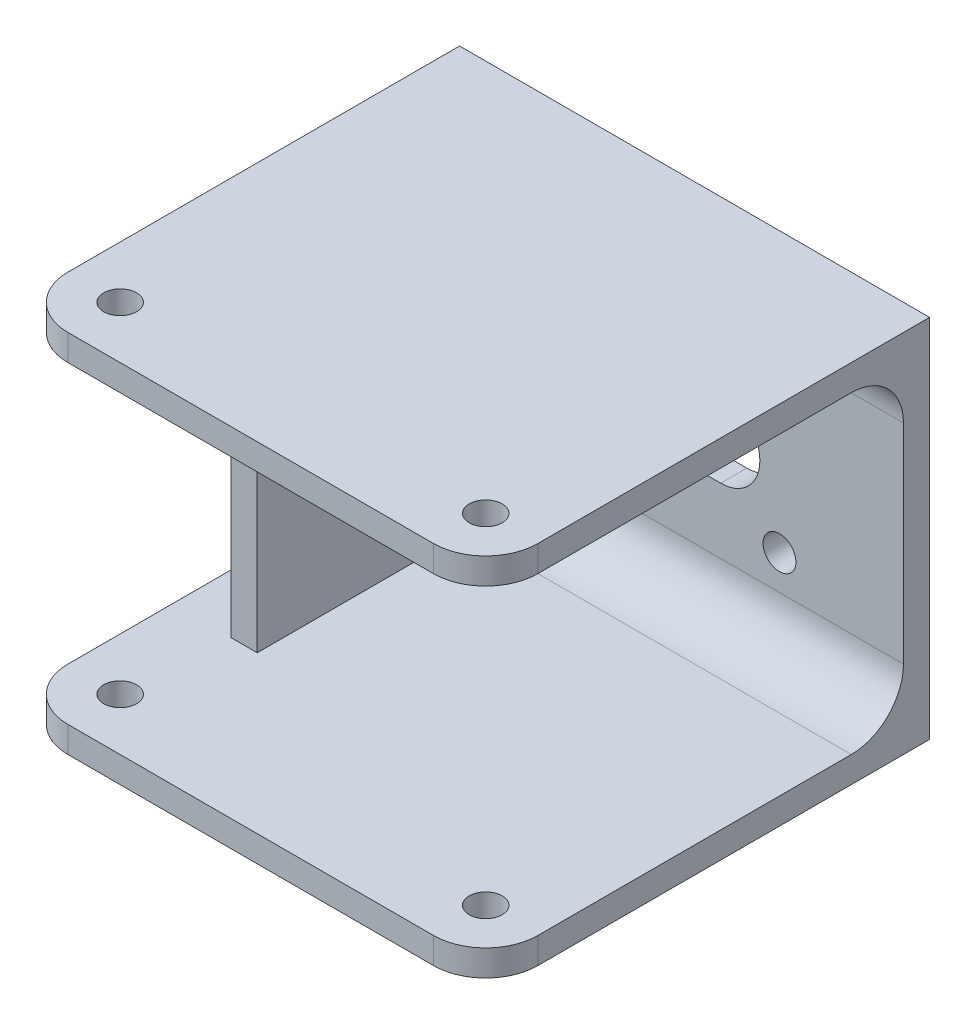
SolidWorks part; units mm, degrees
ref_plane "Front Plane" through (0, 0, 0) normal (0, 0, 1) x (1, 0, 0)
ref_plane "Top Plane" through (0, 0, 0) normal (0, 1, 0) x (1, 0, 0)
ref_plane "Right Plane" through (0, 0, 0) normal (1, 0, 0) x (0, 0, -1)
sketch "Sketch1" plane through (0, 0, 0) normal (0, 0, 1) x (1, 0, 0)
  line L1 (-28.575, -19.05) -> (28.575, -19.05)
  line L2 (-28.575, -19.05) -> (-28.575, 19.05)
  line L3 (-28.575, 19.05) -> (28.575, 19.05)
  line L4 (28.575, -19.05) -> (28.575, 19.05)
  line L5 (-28.575, -19.05) -> (28.575, 19.05) construction
  line L6 (-28.575, 19.05) -> (28.575, -19.05) construction
  point P0 (0, 0)
  dimension "D1" = 38.1
  dimension "D2" = 57.15
extrude "Boss-Extrude1" add sketch "Sketch1" along normal blind 3.175
sketch "Sketch2" plane through (0, 0, 3.175) normal (0, 0, 1) x (1, 0, 0)
  line L0 (-6.35, 0) -> (6.35, 0) construction
  line L1 (-6.35, 4.7625) -> (6.35, 4.7625)
  line L2 (-6.35, -4.7625) -> (6.35, -4.7625)
  line L4 (-13.5, -8.5) -> (13.5, -8.5) construction
  line L5 (-13.5, -8.5) -> (-13.5, 8.5) construction
  line L6 (-13.5, 8.5) -> (13.5, 8.5) construction
  line L7 (13.5, -8.5) -> (13.5, 8.5) construction
  line L8 (-13.5, -8.5) -> (13.5, 8.5) construction
  line L9 (-13.5, 8.5) -> (13.5, -8.5) construction
  arc A0 (-6.35, 4.7625) -> (-6.35, -4.7625) centre (-6.35, 0) ccw
  arc A1 (6.35, -4.7625) -> (6.35, 4.7625) centre (6.35, 0) ccw
  circle A2 centre (-13.5, 8.5) radius 2
  circle A3 centre (13.5, 8.5) radius 2
  circle A4 centre (13.5, -8.5) radius 2
  circle A5 centre (-13.5, -8.5) radius 2
  point P2 (0, 0)
  point P8 (0, 0)
  dimension "D2" = 4.7625
  dimension "D5" = 4
  dimension "D1" = 12.7
  dimension "D3" = 27
  dimension "D4" = 17
extrude "Cut-Extrude1" cut sketch "Sketch2" against normal through all
sketch "Sketch3" plane through (0, 0, 3.175) normal (0, 0, 1) x (1, 0, 0)
  line L0 (-28.575, 19.05) -> (-28.575, -19.05) construction
  line L1 (28.575, 19.05) -> (-28.575, 19.05)
  line L2 (28.575, 19.05) -> (28.575, 22.225)
  line L3 (28.575, 22.225) -> (-28.575, 22.225)
  line L4 (-28.575, 19.05) -> (-28.575, 22.225)
  dimension "D1" = 3.175
extrude "Boss-Extrude2" add sketch "Sketch3" along normal blind 50.8 and the other way up to surface (3.175 mm away) other way up to face at (-11.5, -8.5, 0)
sketch "Sketch5" plane through (0, 19.05, 0) normal (0, -1, 0) x (1, 0, 0)
  line L0 (-22.225, 47.625) -> (22.225, 47.625) construction
  line L1 (28.575, 3.175) -> (-28.575, 3.175) construction
  circle A0 centre (-22.225, 47.625) radius 2
  circle A1 centre (22.225, 47.625) radius 2
  point P2 (0, 47.625)
  dimension "D3" = 4
  dimension "D4" = 4
  dimension "D1" = 44.45
  dimension "D2" = 44.45
extrude "Cut-Extrude2" cut sketch "Sketch5" against normal up to next
fillet "Fillet1" radius 6.35 3 edges at (-28.575, 20.6375, 53.975) (28.575, 20.6375, 53.975) (0, 19.05, 3.175)
mirror "Mirror1" about plane through (0, 0, 0) normal (0, 1, 0) of "Fillet1", "Boss-Extrude2", "Cut-Extrude2"
ref_plane "Plane3" through (-19.8438, 0, 0) normal (1, 0, 0) x (0, 0, -1)
sketch "Sketch7" plane through (-19.8438, 0, 0) normal (-1, 0, 0) x (0, 0, 1)
  line L0 (34.925, 19.05) -> (34.925, -19.05)
  line L1 (9.525, 19.05) -> (47.625, 19.05) construction
  line L2 (9.525, -19.05) -> (47.625, -19.05) construction
  line L4 (3.175, 12.7) -> (3.175, -12.7) construction
  dimension "D1" = 31.75
rib "Rib1" sketch "Sketch7" sketch "Sketch7" thickness 3.175 extrusion direction parallel to sketch draft on no parameters "D1"=3.175
